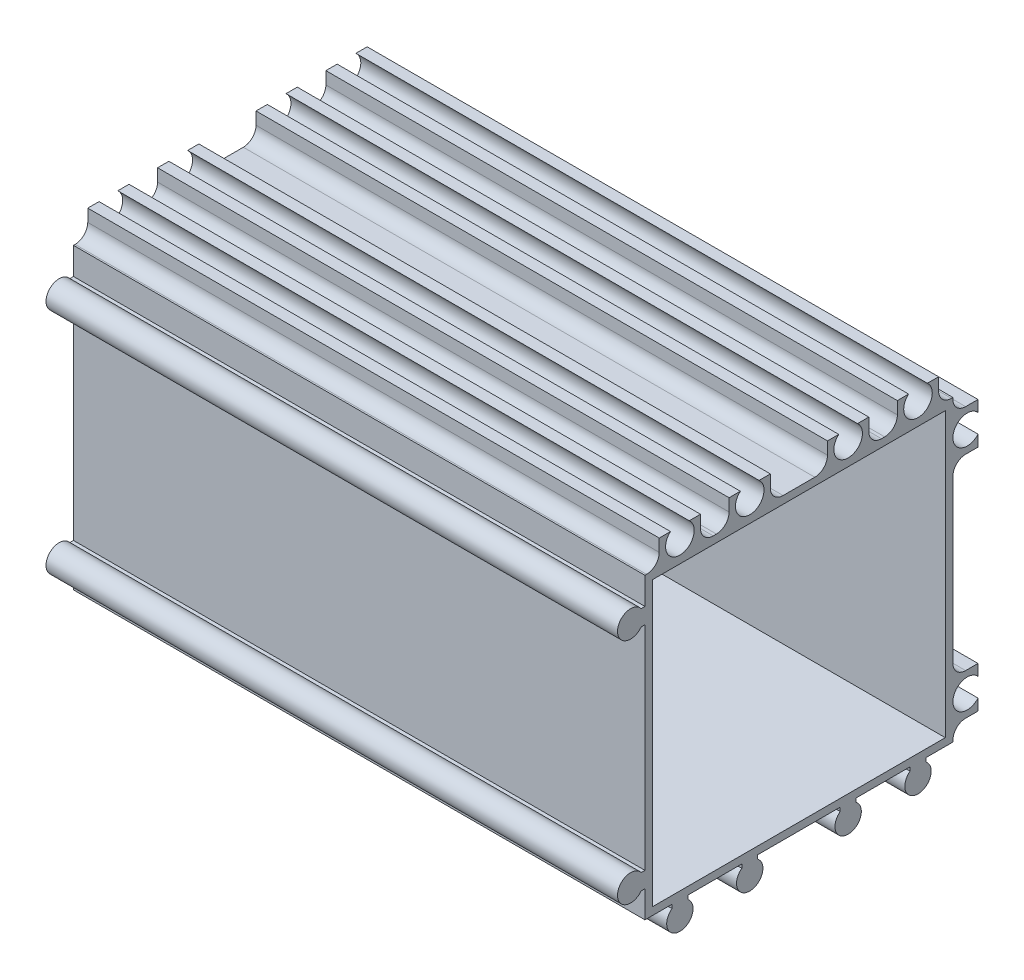
SolidWorks part; units mm, degrees
ref_plane "Спереди" through (0, 0, 0) normal (0, 0, 1) x (1, 0, 0)
ref_plane "Сверху" through (0, 0, 0) normal (0, 1, 0) x (1, 0, 0)
ref_plane "Справа" through (0, 0, 0) normal (1, 0, 0) x (0, 0, -1)
ref_plane "Плоскость4" through (90, 0, 0) normal (1, 0, 0) x (0, 0, -1)
sketch "Эскиз1" plane through (90, 0, 0) normal (1, 0, 0) x (0, 0, -1)
  line L0 (6.75, 160.9062) -> (6.75, 204.25)
  line L1 (6.75, 204.25) -> (-38.0938, 204.25)
  line L2 (-38.0938, 201.75) -> (-37.5, 201.75)
  line L3 (-37.5, 201.75) -> (-37.5, 168.25)
  line L4 (-37.5, 168.25) -> (-38.0938, 168.25)
  line L5 (-38.0938, 165.75) -> (-37.5, 165.75)
  line L6 (-37.5, 165.75) -> (-37.5, 161.5)
  line L7 (-37.5, 161.5) -> (-33.25, 161.5)
  line L8 (-33.25, 161.5) -> (-33.25, 160.9062)
  line L9 (-30.75, 160.9062) -> (-30.75, 161.5)
  line L10 (-30.75, 161.5) -> (-22.25, 161.5)
  line L11 (-22.25, 161.5) -> (-22.25, 160.9062)
  line L12 (-19.75, 160.9062) -> (-19.75, 161.5)
  line L13 (-19.75, 161.5) -> (-6.75, 161.5)
  line L14 (-6.75, 161.5) -> (-6.75, 160.9062)
  line L15 (-4.25, 160.9062) -> (-4.25, 161.5)
  line L16 (-4.25, 161.5) -> (4.25, 161.5)
  line L17 (4.25, 161.5) -> (4.25, 160.9062)
  arc A0 (-38.0938, 204.25) -> (-38.0938, 201.75) centre (-39.75, 203) ccw
  arc A1 (-38.0938, 168.25) -> (-38.0938, 165.75) centre (-39.75, 167) ccw
  arc A2 (-33.25, 160.9062) -> (-30.75, 160.9062) centre (-32, 159.25) ccw
  arc A3 (-22.25, 160.9062) -> (-19.75, 160.9062) centre (-21, 159.25) ccw
  arc A4 (-6.75, 160.9062) -> (-4.25, 160.9062) centre (-5.5, 159.25) ccw
  arc A5 (4.25, 160.9062) -> (6.75, 160.9062) centre (5.5, 159.25) ccw
extrude "Бобышка-Вытянуть1" add sketch "Эскиз1" against normal blind 90
sketch "Эскиз2" plane through (0, 0, -6.75) normal (0, 0, -1) x (-1, 0, 0)
  line L0 (0, 204.25) -> (0, 161.5)
  line L1 (0, 161.5) -> (-90, 161.5)
  line L2 (-90, 161.5) -> (-90, 204.25)
  line L3 (-90, 204.25) -> (0, 204.25)
extrude "Бобышка-Вытянуть2" add sketch "Эскиз2" along normal blind 8.2
sketch "Эскиз3" plane through (0, 204.25, 0) normal (0, 1, 0) x (-1, 0, 0)
  line L0 (-90, -14.95) -> (-90, 37.5)
  line L1 (-90, 37.5) -> (0, 37.5)
  line L2 (0, 37.5) -> (0, -14.95)
  line L3 (0, -14.95) -> (-90, -14.95)
extrude "Бобышка-Вытянуть3" add sketch "Эскиз3" along normal blind 8.2
sketch "Эскиз4" plane through (0, 0, 0) normal (-1, 0, 0) x (0, 0, 1)
  line L0 (-14.95, 161.5) -> (-11, 161.5)
  line L1 (-11, 161.5) -> (-11, 163.75)
  line L2 (-11, 163.75) -> (-14.95, 163.75)
  line L3 (-14.95, 163.75) -> (-14.95, 161.5)
extrude "Вырез-Вытянуть1" cut sketch "Эскиз4" against normal through all
sketch "Эскиз5" plane through (0, 0, 0) normal (-1, 0, 0) x (0, 0, 1)
  line L0 (-14.95, 170.25) -> (-11, 170.25)
  line L1 (-11, 170.25) -> (-11, 199.75)
  line L2 (-11, 199.75) -> (-14.95, 199.75)
  line L3 (-14.95, 199.75) -> (-14.95, 170.25)
extrude "Вырез-Вытянуть2" cut sketch "Эскиз5" against normal through all
sketch "Эскиз6" plane through (0, 0, 0) normal (-1, 0, 0) x (0, 0, 1)
  line L0 (-14.95, 212.45) -> (-14.95, 206.25)
  line L1 (-14.95, 206.25) -> (-11, 206.25)
  line L2 (-11, 206.25) -> (-11, 212.45)
  line L3 (-11, 212.45) -> (-14.95, 212.45)
extrude "Вырез-Вытянуть3" cut sketch "Эскиз6" against normal through all
sketch "Эскиз7" plane through (0, 0, 0) normal (-1, 0, 0) x (0, 0, 1)
  line L0 (-11, 212.45) -> (-11, 208.5)
  line L1 (-11, 208.5) -> (-8.75, 208.5)
  line L2 (-8.75, 208.5) -> (-8.75, 212.45)
  line L3 (-8.75, 212.45) -> (-11, 212.45)
extrude "Вырез-Вытянуть4" cut sketch "Эскиз7" against normal through all
sketch "Эскиз8" plane through (0, 0, 0) normal (-1, 0, 0) x (0, 0, 1)
  line L0 (-2.25, 212.45) -> (-2.25, 208.5)
  line L1 (-2.25, 208.5) -> (2.25, 208.5)
  line L2 (2.25, 208.5) -> (2.25, 212.45)
  line L3 (2.25, 212.45) -> (-2.25, 212.45)
extrude "Вырез-Вытянуть5" cut sketch "Эскиз8" against normal through all
sketch "Эскиз9" plane through (0, 0, 0) normal (-1, 0, 0) x (0, 0, 1)
  line L0 (8.75, 212.45) -> (8.75, 208.5)
  line L1 (8.75, 208.5) -> (17.75, 208.5)
  line L2 (17.75, 208.5) -> (17.75, 212.45)
  line L3 (17.75, 212.45) -> (8.75, 212.45)
extrude "Вырез-Вытянуть6" cut sketch "Эскиз9" against normal through all
sketch "Эскиз10" plane through (0, 0, 0) normal (-1, 0, 0) x (0, 0, 1)
  line L0 (24.25, 212.45) -> (24.25, 208.5)
  line L1 (24.25, 208.5) -> (28.75, 208.5)
  line L2 (28.75, 208.5) -> (28.75, 212.45)
  line L3 (28.75, 212.45) -> (24.25, 212.45)
extrude "Вырез-Вытянуть7" cut sketch "Эскиз10" against normal through all
sketch "Эскиз11" plane through (0, 0, 0) normal (-1, 0, 0) x (0, 0, 1)
  line L0 (37.5, 212.45) -> (35.25, 212.45)
  line L1 (35.25, 212.45) -> (35.25, 208.5)
  line L2 (35.25, 208.5) -> (37.5, 208.5)
  line L3 (37.5, 208.5) -> (37.5, 212.45)
extrude "Вырез-Вытянуть8" cut sketch "Эскиз11" against normal through all
sketch "Эскиз12" plane through (90, 0, 0) normal (1, 0, 0) x (0, 0, -1)
  line L0 (9.8, 207.3) -> (-36.3, 207.3)
  line L1 (-36.3, 207.3) -> (-36.3, 162.7)
  line L2 (-36.3, 162.7) -> (9.8, 162.7)
  line L3 (9.8, 162.7) -> (9.8, 207.3)
  line L4 (11, 170.25) -> (11, 199.75) construction
  line L5 (-37.5, 201.75) -> (-37.5, 168.25) construction
  line L6 (-8.75, 208.5) -> (-17.75, 208.5) construction
  line L7 (-19.75, 161.5) -> (-6.75, 161.5) construction
  dimension "D1" = 1.2
  dimension "D2" = 1.2
  dimension "D3" = 1.2
  dimension "D4" = 1.2
extrude "Вырез-Вытянуть9" cut sketch "Эскиз12" against normal blind 86.2
hole_wizard "Диаметр отверстия Ø2.5 (2.5)1" positions "Эскиз14" profile "Эскиз13" hole size "Ø2.5" standard "Ansi Metric"
sketch "Эскиз14" plane through (90, 0, 0) normal (1, 0, 0) x (0, 0, -1)
  point P0 (5.5, 159.25)
  point P1 (-21, 159.25)
  point P2 (-5.5, 159.25)
  point P3 (-32, 159.25)
  point P4 (-39.75, 167)
  point P5 (-39.75, 203)
sketch "Эскиз13" plane through (90, 159.25, -5.5) normal (0, 1, 0) x (0, 0, -1)
  line L0 (0, 0) -> (0, 90)
  line L1 (0, 90) -> (1.25, 90)
  line L2 (1.25, 90) -> (1.25, 0)
  line L5 (1.25, 0) -> (0, 0)
  line L11 (0, -6.35) -> (0, 107.95) construction
  dimension "Диаметр сквозного отверстия" = 2.5
  dimension "Глубина сквозного отверстия" = 90
hole_wizard "Диаметр отверстия Ø4.5 (4.5)1" positions "Эскиз16" profile "Эскиз15" hole size "Ø4.5" standard "Ansi Metric"
sketch "Эскиз16" plane through (0, 0, 0) normal (-1, 0, 0) x (0, 0, 1)
  point P0 (-13.25, 167)
  point P1 (-13.25, 203)
  point P2 (-5.5, 210.75)
  point P3 (5.5, 210.75)
  point P4 (21, 210.75)
  point P5 (32, 210.75)
sketch "Эскиз15" plane through (0, 167, -13.25) normal (0, 1, 0) x (0, 0, 1)
  line L0 (0, 0) -> (0, 90)
  line L1 (0, 90) -> (2.25, 90)
  line L2 (2.25, 90) -> (2.25, 0)
  line L5 (2.25, 0) -> (0, 0)
  line L11 (0, -6.35) -> (0, 107.95) construction
  dimension "Диаметр сквозного отверстия" = 4.5
  dimension "Глубина сквозного отверстия" = 90
hole_wizard "Диаметр отверстия Ø8.3 (8.3)1" [suppressed] positions "Эскиз18" profile "Эскиз17" hole size "Ø8.3" standard "Ansi Metric"
sketch "Эскиз18" plane through (0, 0, 0) normal (-1, 0, 0) x (0, 0, 1)
  point P0 (13.25, 185)
sketch "Эскиз17" plane through (0, 185, 13.25) normal (0, 1, 0) x (0, 0, 1)
  line L0 (0, 0) -> (0, 3.2)
  line L1 (0, 3.2) -> (4.15, 3.2)
  line L2 (4.15, 3.2) -> (4.15, 0)
  line L5 (4.15, 0) -> (0, 0)
  line L10 (0, 3.2) -> (-4.15, 3.2) construction
  line L11 (0, -6.35) -> (0, 107.95) construction
  dimension "Диаметр отверстия" = 8.3
  dimension "Глубина отверстия" = 3.2
  dimension "Угол заточки сверла" = 180
sketch "Эскиз19" plane through (90, 0, 0) normal (1, 0, 0) x (0, 0, -1)
  circle A0 centre (-39.75, 203) radius 1.6725
  circle A1 centre (-39.75, 167) radius 1.4592
  circle A2 centre (-32, 159.25) radius 1.4599
  circle A3 centre (-21, 159.25) radius 1.5928
  circle A4 centre (-5.5, 159.25) radius 1.5322
  circle A5 centre (5.5, 159.25) radius 1.5961
extrude "Бобышка-Вытянуть4" add sketch "Эскиз19" against normal blind 90
sketch "Эскиз20" [suppressed] plane through (0, 0, 0) normal (-1, 0, 0) x (0, 0, 1)
  circle A0 centre (13.25, 185) radius 4.15
extrude "Вырез-Вытянуть10" [suppressed] cut sketch "Эскиз20" against normal blind 90
fillet "Скругление1" radius 2 1 edges at (45, 208.5, -8.75)
fillet "Скругление2" radius 2 1 edges at (45, 163.75, -11)
fillet "Скругление3" radius 2 1 edges at (45, 170.25, -11)
fillet "Скругление4" radius 2 1 edges at (45, 199.75, -11)
fillet "Скругление5" radius 2 1 edges at (45, 206.25, -11)
fillet "Скругление6" radius 2 1 edges at (45, 208.5, -2.25)
fillet "Скругление7" radius 2 1 edges at (45, 208.5, 2.25)
fillet "Скругление8" radius 2 1 edges at (45, 208.5, 8.75)
fillet "Скругление9" radius 2 1 edges at (45, 208.5, 17.75)
fillet "Скругление10" radius 2 1 edges at (45, 208.5, 24.25)
fillet "Скругление11" radius 2 1 edges at (45, 208.5, 28.75)
fillet "Скругление12" radius 2 1 edges at (45, 208.5, 35.25)
equation "\"D2@Эскиз12\"=\"D1@Эскиз12\""
equation "\"D3@Эскиз12\"=\"D1@Эскиз12\""
equation "\"D4@Эскиз12\"=\"D1@Эскиз12\""
